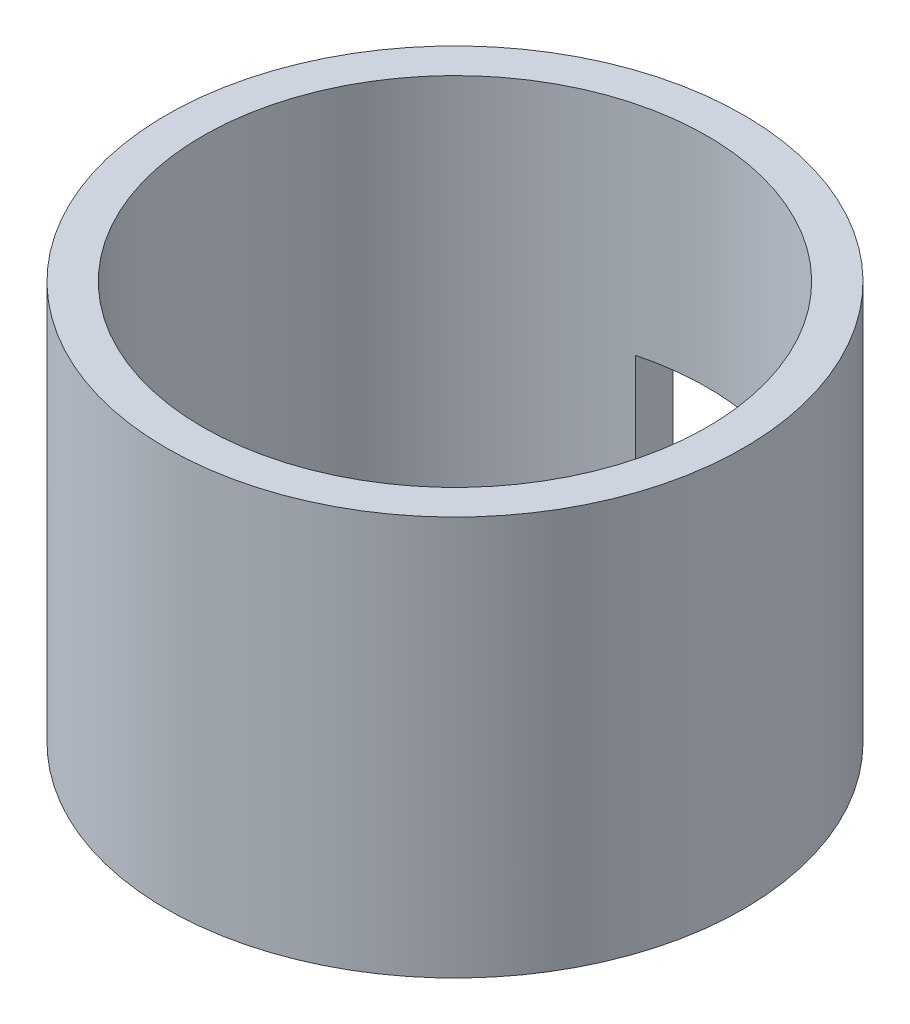
SolidWorks part; units mm, degrees
ref_plane "Alzado" through (0, 0, 0) normal (0, 0, 1) x (1, 0, 0)
ref_plane "Planta" through (0, 0, 0) normal (0, 1, 0) x (1, 0, 0)
ref_plane "Vista lateral" through (0, 0, 0) normal (1, 0, 0) x (0, 0, -1)
sketch "Croquis1" plane through (0, 0, 0) normal (0, 1, 0) x (1, 0, 0)
  circle A6 centre (0, 0) radius 13.9
  circle A7 centre (0, 0) radius 15.9
  dimension "D1" = 27.8
  dimension "D2" = 2
extrude "Saliente-Extruir1" add sketch "Croquis1" along normal blind 22
sketch "Croquis2" plane through (0, 0, 0) normal (0, 0, 1) x (1, 0, 0)
  line L1 (-3.5, -10) -> (3.5, -10)
  line L2 (-3.5, -10) -> (-3.5, 10)
  line L3 (-3.5, 10) -> (3.5, 10)
  line L4 (3.5, -10) -> (3.5, 10)
  line L5 (-3.5, -10) -> (3.5, 10) construction
  line L6 (-3.5, 10) -> (3.5, -10) construction
  point P0 (0, 0)
  dimension "D1" = 7
  dimension "D2" = 20
extrude "Cortar-Extruir1" cut sketch "Croquis2" against normal blind 22
